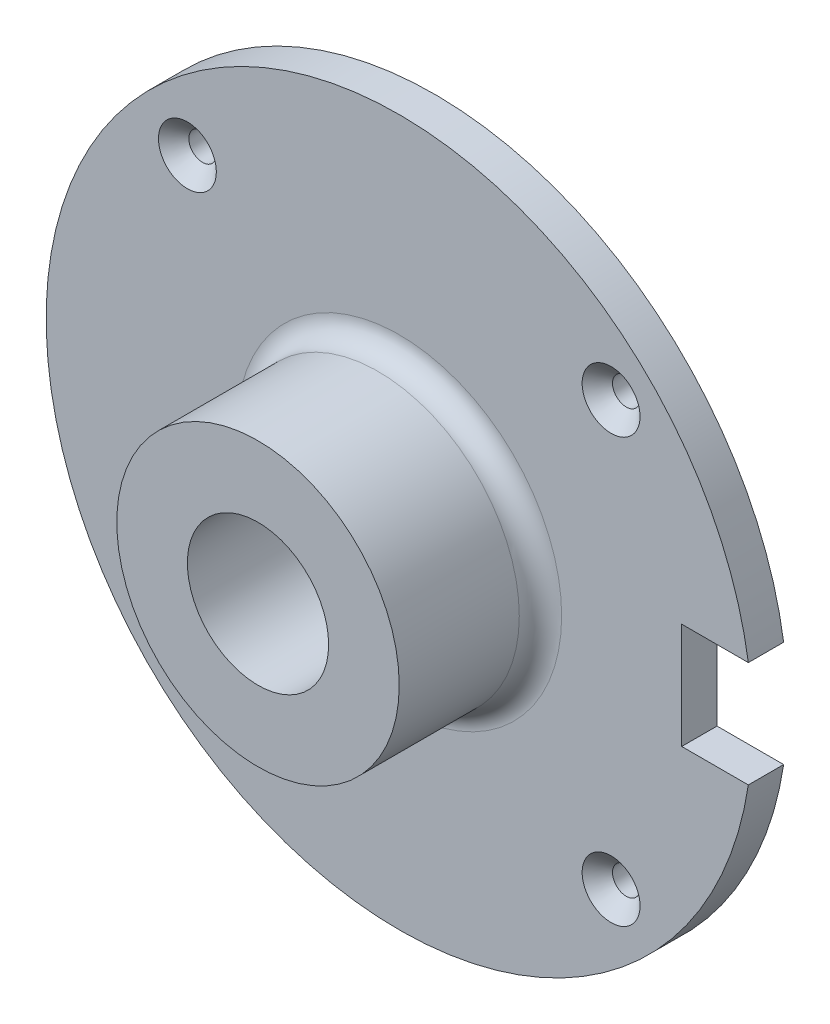
SolidWorks part; units mm, degrees
ref_plane "Front Plane" through (0, 0, 0) normal (0, 0, 1) x (1, 0, 0)
ref_plane "Top Plane" through (0, 0, 0) normal (0, 1, 0) x (1, 0, 0)
ref_plane "Right Plane" through (0, 0, 0) normal (1, 0, 0) x (0, 0, -1)
other "Configuration Table"
sketch "Sketch1" plane through (0, 0, 0) normal (1, 0, 0) x (0, 0, -1)
  line L0 (0, 10) -> (-25, 10)
  line L1 (-25, 10) -> (-25, 20)
  line L2 (-25, 20) -> (-8, 20)
  line L5 (-5, 23) -> (-5, 50)
  line L6 (-5, 50) -> (0, 50)
  line L7 (0, 50) -> (0, 10)
  line L8 (-50, 0) -> (20, 0) construction
  arc A0 (-8, 20) -> (-5, 23) centre (-8, 23) ccw
  dimension "D9" = 3
  dimension "D1" = 25
  dimension "D2" = 5
  dimension "D3" = 20
  dimension "D6" = 50
  dimension "D7" = 10
revolve "Revolve1" add sketch "Sketch1" angle 360 about L8
sketch "Sketch5" plane through (0, 0, 5) normal (0, 0, 1) x (1, 0, 0)
  line L1 (40, -7.5) -> (50, -7.5)
  line L2 (40, -7.5) -> (40, 7.5)
  line L3 (40, 7.5) -> (50, 7.5)
  line L4 (50, -7.5) -> (50, 7.5)
  circle A0 centre (0, 0) radius 50 construction
  point P4 (40, 0)
  dimension "D1" = 15
  dimension "D2" = 10
extrude "Extrude2" cut sketch "Sketch5" against normal through all
hole_wizard "CSK for M3.5 Flat Head Machine Screw1" positions "Sketch7" profile "Sketch6" countersink size "M3.5" standard "Ansi Metric" end condition through all
sketch "Sketch7" plane through (0, 0, 5) normal (0, 0, 1) x (1, 0, 0)
  point P0 (-30, 30)
  dimension "D1" = 30
  dimension "D2" = 30
sketch "Sketch6" plane through (-30, 30, 5) normal (1, 0, 0) x (0, -1, 0)
  line L0 (0, 0) -> (0, 5)
  line L1 (0, 5) -> (1.95, 5)
  line L2 (1.95, 5) -> (1.95, 2.15)
  line L3 (1.95, 2.15) -> (4.1, 0)
  line L5 (4.1, 0) -> (0, 0)
  line L6 (-1.95, 2.15) -> (-4.1, 0) construction
  line L11 (0, -6.35) -> (0, 107.95) construction
  dimension "Thru Hole Dia." = 3.9
  dimension "Thru Hole Depth" = 5
  dimension "Near C'Sink Dia." = 8.2
  dimension "Near C'Sink Angle" = 90
pattern_circular "CirPattern1" count 4 over 360 about axis through (0, 0, 0) along (0, 0, 1) of "CSK for M3.5 Flat Head Machine Screw1"
